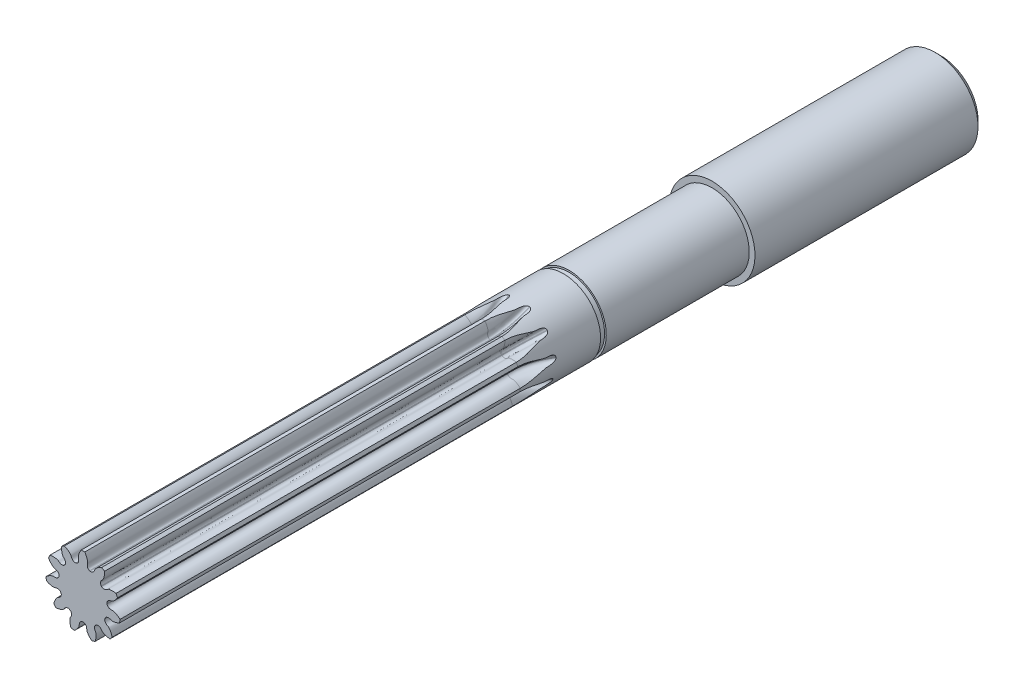
SolidWorks part; units mm, degrees
ref_plane "Спереди" through (0, 0, 0) normal (0, 0, 1) x (1, 0, 0)
ref_plane "Сверху" through (0, 0, 0) normal (0, 1, 0) x (1, 0, 0)
ref_plane "Справа" through (0, 0, 0) normal (1, 0, 0) x (0, 0, -1)
other "Configuration Table"
sketch "Эскиз1" plane through (0, 0, 0) normal (0, 0, 1) x (1, 0, 0)
  line L0 (0, 4.2505) -> (0, 6.5001) construction
  arc A6 (0.303, 6.493) -> (-0.303, 6.493) centre (0, 0) ccw
  arc A8 (3.7653, 5.2984) -> (3.2555, 5.6261) centre (0, 0) ccw
  arc A9 (6.0321, 2.4217) -> (5.7804, 2.9729) centre (0, 0) ccw
  arc A10 (6.3838, -1.224) -> (6.47, -0.6241) centre (0, 0) ccw
  arc A11 (4.7087, -4.481) -> (5.1055, -4.023) centre (0, 0) ccw
  arc A12 (1.5386, -6.3154) -> (2.12, -6.1446) centre (0, 0) ccw
  arc A13 (-2.12, -6.1446) -> (-1.5386, -6.3154) centre (0, 0) ccw
  arc A14 (-5.1055, -4.023) -> (-4.7087, -4.481) centre (0, 0) ccw
  arc A15 (-6.47, -0.6241) -> (-6.3838, -1.224) centre (0, 0) ccw
  arc A16 (-5.7804, 2.9729) -> (-6.0321, 2.4217) centre (0, 0) ccw
  arc A17 (-3.2555, 5.6261) -> (-3.7653, 5.2984) centre (0, 0) ccw
  arc A18 (-4.1999, 0.6538) -> (-4.214, 0.5559) centre (0, 0) ccw
  arc A19 (-3.1797, 2.8207) -> (-3.2445, 2.746) centre (0, 0) ccw
  arc A20 (-1.15, 4.092) -> (-1.2449, 4.0641) centre (0, 0) ccw
  arc A21 (1.2449, 4.0641) -> (1.15, 4.092) centre (0, 0) ccw
  arc A22 (3.2445, 2.746) -> (3.1797, 2.8207) centre (0, 0) ccw
  arc A23 (4.214, 0.5559) -> (4.1999, 0.6538) centre (0, 0) ccw
  arc A24 (3.8456, -1.8106) -> (3.8867, -1.7206) centre (0, 0) ccw
  arc A25 (2.2563, -3.6023) -> (2.3394, -3.5488) centre (0, 0) ccw
  arc A26 (-0.0494, -4.2502) -> (0.0494, -4.2502) centre (0, 0) ccw
  arc A27 (-2.3394, -3.5488) -> (-2.2563, -3.6023) centre (0, 0) ccw
  arc A28 (-3.8867, -1.7206) -> (-3.8456, -1.8106) centre (0, 0) ccw
  spline S0 degree 3 poles (0.303, 6.493) (0.3466, 6.4296) (0.4149, 6.3229) (0.5038, 6.1711) (0.5716, 6.0406) (0.6313, 5.9095) (0.6852, 5.7791) (0.7296, 5.6484) (0.7674, 5.5183) (0.798, 5.3728) (0.8278, 5.1961) (0.7682, 4.9723) (0.7367, 4.7556) (0.754, 4.5684) (0.7852, 4.4471) (0.829, 4.3517) (0.8776, 4.2755) (0.9328, 4.2146) (1.0177, 4.1438) (1.0937, 4.1064) (1.15, 4.092) knots 0 0 0 0 0.085617 0.14097 0.195721 0.24917 0.301247 0.352629 0.402768 0.451734 0.518548 0.599046 0.705842 0.760988 0.807057 0.844573 0.877292 0.907236 0.935686 1 1 1 1
  spline S1 degree 3 poles (-0.303, 6.493) (-0.3466, 6.4296) (-0.4149, 6.3229) (-0.5038, 6.1711) (-0.5716, 6.0406) (-0.6313, 5.9095) (-0.6852, 5.7791) (-0.7296, 5.6484) (-0.7674, 5.5183) (-0.798, 5.3728) (-0.8278, 5.1961) (-0.7682, 4.9723) (-0.7367, 4.7556) (-0.754, 4.5684) (-0.7852, 4.4471) (-0.829, 4.3517) (-0.8776, 4.2755) (-0.9328, 4.2146) (-1.0177, 4.1438) (-1.0937, 4.1064) (-1.15, 4.092) knots 0 0 0 0 0.085617 0.14097 0.195721 0.24917 0.301247 0.352629 0.402768 0.451734 0.518548 0.599046 0.705842 0.760988 0.807057 0.844573 0.877292 0.907236 0.935686 1 1 1 1
  spline S2 degree 3 poles (3.2555, 5.6261) (3.1845, 5.5963) (3.0694, 5.5435) (2.9125, 5.4638) (2.7849, 5.3907) (2.6639, 5.3126) (2.548, 5.2321) (2.4399, 5.1462) (2.3379, 5.0572) (2.2335, 4.9513) (2.1128, 4.8187) (2.042, 4.5983) (1.9513, 4.399) (1.8356, 4.2508) (1.7437, 4.1657) (1.6553, 4.1091) (1.5733, 4.0713) (1.4939, 4.0498) (1.3841, 4.0362) (1.3, 4.0458) (1.2449, 4.0641) knots 0 0 0 0 0.085617 0.14097 0.195721 0.24917 0.301247 0.352629 0.402768 0.451734 0.518548 0.599046 0.705842 0.760988 0.807057 0.844573 0.877292 0.907236 0.935686 1 1 1 1
  spline S3 degree 3 poles (3.7653, 5.2984) (3.7677, 5.2215) (3.7674, 5.0948) (3.7602, 4.9191) (3.7467, 4.7726) (3.7259, 4.6301) (3.7008, 4.4913) (3.6676, 4.3573) (3.629, 4.2274) (3.5761, 4.0885) (3.5056, 3.9237) (3.3345, 3.7676) (3.1908, 3.6024) (3.1041, 3.4356) (3.0649, 3.3166) (3.0502, 3.2127) (3.0498, 3.1224) (3.0633, 3.0412) (3.0965, 2.9357) (3.1402, 2.8632) (3.1797, 2.8207) knots 0 0 0 0 0.085617 0.14097 0.195721 0.24917 0.301247 0.352629 0.402768 0.451734 0.518548 0.599046 0.705842 0.760988 0.807057 0.844573 0.877292 0.907236 0.935686 1 1 1 1
  spline S4 degree 3 poles (5.7804, 2.9729) (5.7046, 2.9862) (5.5791, 3.004) (5.4041, 3.0219) (5.2573, 3.0293) (5.1132, 3.0291) (4.9722, 3.024) (4.8349, 3.0101) (4.7009, 2.9904) (4.5558, 2.9578) (4.3826, 2.9115) (4.2038, 2.7644) (4.0198, 2.6457) (3.8424, 2.5836) (3.719, 2.5617) (3.6141, 2.5619) (3.5246, 2.5744) (3.4462, 2.5993) (3.3465, 2.6472) (3.281, 2.7007) (3.2445, 2.746) knots 0 0 0 0 0.085617 0.14097 0.195721 0.24917 0.301247 0.352629 0.402768 0.451734 0.518548 0.599046 0.705842 0.760988 0.807057 0.844573 0.877292 0.907236 0.935686 1 1 1 1
  spline S5 degree 3 poles (6.0321, 2.4217) (5.9925, 2.3557) (5.9238, 2.2492) (5.8227, 2.1053) (5.7322, 1.9894) (5.6377, 1.8807) (5.5415, 1.7775) (5.4411, 1.6827) (5.3384, 1.5943) (5.2188, 1.5061) (5.0704, 1.4055) (4.8421, 1.3668) (4.6319, 1.3054) (4.4688, 1.212) (4.3714, 1.1331) (4.3029, 1.0537) (4.2537, 0.9778) (4.2212, 0.9023) (4.1921, 0.7956) (4.1897, 0.711) (4.1999, 0.6538) knots 0 0 0 0 0.085617 0.14097 0.195721 0.24917 0.301247 0.352629 0.402768 0.451734 0.518548 0.599046 0.705842 0.760988 0.807057 0.844573 0.877292 0.907236 0.935686 1 1 1 1
  spline S6 degree 3 poles (6.47, -0.6241) (6.4135, -0.572) (6.3176, -0.4892) (6.18, -0.3795) (6.0605, -0.2938) (5.9391, -0.2162) (5.8178, -0.1442) (5.6948, -0.0816) (5.5714, -0.0258) (5.4317, 0.0252) (5.261, 0.0799) (5.031, 0.0528) (4.812, 0.0524) (4.6292, 0.0961) (4.5136, 0.1444) (4.4254, 0.2013) (4.3569, 0.2602) (4.3044, 0.3235) (4.2465, 0.4177) (4.2203, 0.4982) (4.214, 0.5559) knots 0 0 0 0 0.085617 0.14097 0.195721 0.24917 0.301247 0.352629 0.402768 0.451734 0.518548 0.599046 0.705842 0.760988 0.807057 0.844573 0.877292 0.907236 0.935686 1 1 1 1
  spline S7 degree 3 poles (6.3838, -1.224) (6.3148, -1.2581) (6.1995, -1.3105) (6.0366, -1.3769) (5.8978, -1.4255) (5.7595, -1.4658) (5.6228, -1.5007) (5.4871, -1.5261) (5.3529, -1.5449) (5.2046, -1.5545) (5.0254, -1.5588) (4.8124, -1.468) (4.6023, -1.406) (4.4146, -1.3964) (4.2901, -1.4101) (4.1895, -1.4399) (4.1071, -1.4771) (4.0389, -1.5231) (3.9568, -1.5971) (3.909, -1.667) (3.8867, -1.7206) knots 0 0 0 0 0.085617 0.14097 0.195721 0.24917 0.301247 0.352629 0.402768 0.451734 0.518548 0.599046 0.705842 0.760988 0.807057 0.844573 0.877292 0.907236 0.935686 1 1 1 1
  spline S8 degree 3 poles (5.1055, -4.023) (5.0861, -3.9486) (5.0502, -3.827) (4.9937, -3.6604) (4.9395, -3.5237) (4.8795, -3.3928) (4.8163, -3.2667) (4.7466, -3.1475) (4.673, -3.0338) (4.5831, -2.9154) (4.469, -2.7771) (4.2609, -2.6756) (4.0765, -2.5575) (3.9463, -2.4219) (3.8751, -2.3188) (3.8317, -2.2233) (3.8059, -2.1366) (3.796, -2.055) (3.7981, -1.9445) (3.8196, -1.8626) (3.8456, -1.8106) knots 0 0 0 0 0.085617 0.14097 0.195721 0.24917 0.301247 0.352629 0.402768 0.451734 0.518548 0.599046 0.705842 0.760988 0.807057 0.844573 0.877292 0.907236 0.935686 1 1 1 1
  spline S9 degree 3 poles (4.7087, -4.481) (4.6322, -4.4724) (4.5068, -4.4542) (4.3339, -4.422) (4.1908, -4.3878) (4.0527, -4.3469) (3.9189, -4.3023) (3.791, -4.2503) (3.6679, -4.1937) (3.538, -4.1215) (3.3848, -4.0283) (3.2547, -3.8367) (3.1116, -3.671) (2.9588, -3.5615) (2.8467, -3.5057) (2.7459, -3.4763) (2.6565, -3.4631) (2.5743, -3.4649) (2.4652, -3.4828) (2.3872, -3.5157) (2.3394, -3.5488) knots 0 0 0 0 0.085617 0.14097 0.195721 0.24917 0.301247 0.352629 0.402768 0.451734 0.518548 0.599046 0.705842 0.760988 0.807057 0.844573 0.877292 0.907236 0.935686 1 1 1 1
  spline S10 degree 3 poles (2.12, -6.1446) (2.144, -6.0715) (2.1795, -5.9499) (2.222, -5.7792) (2.2503, -5.6349) (2.2706, -5.4922) (2.2856, -5.352) (2.2914, -5.214) (2.291, -5.0786) (2.2793, -4.9304) (2.2582, -4.7524) (2.138, -4.5545) (2.0467, -4.3554) (2.0105, -4.1709) (2.0063, -4.0457) (2.0215, -3.9419) (2.0466, -3.8551) (2.0824, -3.7811) (2.144, -3.6892) (2.2063, -3.6319) (2.2563, -3.6023) knots 0 0 0 0 0.085617 0.14097 0.195721 0.24917 0.301247 0.352629 0.402768 0.451734 0.518548 0.599046 0.705842 0.760988 0.807057 0.844573 0.877292 0.907236 0.935686 1 1 1 1
  spline S11 degree 3 poles (1.5386, -6.3154) (1.4789, -6.2668) (1.3833, -6.1836) (1.2552, -6.0631) (1.1533, -5.957) (1.0592, -5.8479) (0.9707, -5.738) (0.8913, -5.6252) (0.8184, -5.511) (0.7481, -5.38) (0.6696, -5.2188) (0.6638, -4.9873) (0.6329, -4.7705) (0.5636, -4.5958) (0.4995, -4.4882) (0.4306, -4.409) (0.3625, -4.3496) (0.2924, -4.3067) (0.1909, -4.2627) (0.1075, -4.2482) (0.0494, -4.2502) knots 0 0 0 0 0.085617 0.14097 0.195721 0.24917 0.301247 0.352629 0.402768 0.451734 0.518548 0.599046 0.705842 0.760988 0.807057 0.844573 0.877292 0.907236 0.935686 1 1 1 1
  spline S12 degree 3 poles (-1.5386, -6.3154) (-1.4789, -6.2668) (-1.3833, -6.1836) (-1.2552, -6.0631) (-1.1533, -5.957) (-1.0592, -5.8479) (-0.9707, -5.738) (-0.8913, -5.6252) (-0.8184, -5.511) (-0.7481, -5.38) (-0.6696, -5.2188) (-0.6638, -4.9873) (-0.6329, -4.7705) (-0.5636, -4.5958) (-0.4995, -4.4882) (-0.4306, -4.409) (-0.3625, -4.3496) (-0.2924, -4.3067) (-0.1909, -4.2627) (-0.1075, -4.2482) (-0.0494, -4.2502) knots 0 0 0 0 0.085617 0.14097 0.195721 0.24917 0.301247 0.352629 0.402768 0.451734 0.518548 0.599046 0.705842 0.760988 0.807057 0.844573 0.877292 0.907236 0.935686 1 1 1 1
  spline S13 degree 3 poles (-2.12, -6.1446) (-2.144, -6.0715) (-2.1795, -5.9499) (-2.222, -5.7792) (-2.2503, -5.6349) (-2.2706, -5.4922) (-2.2856, -5.352) (-2.2914, -5.214) (-2.291, -5.0786) (-2.2793, -4.9304) (-2.2582, -4.7524) (-2.138, -4.5545) (-2.0467, -4.3554) (-2.0105, -4.1709) (-2.0063, -4.0457) (-2.0215, -3.9419) (-2.0466, -3.8551) (-2.0824, -3.7811) (-2.144, -3.6892) (-2.2063, -3.6319) (-2.2563, -3.6023) knots 0 0 0 0 0.085617 0.14097 0.195721 0.24917 0.301247 0.352629 0.402768 0.451734 0.518548 0.599046 0.705842 0.760988 0.807057 0.844573 0.877292 0.907236 0.935686 1 1 1 1
  spline S14 degree 3 poles (-4.7087, -4.481) (-4.6322, -4.4724) (-4.5068, -4.4542) (-4.3339, -4.422) (-4.1908, -4.3878) (-4.0527, -4.3469) (-3.9189, -4.3023) (-3.791, -4.2503) (-3.6679, -4.1937) (-3.538, -4.1215) (-3.3848, -4.0283) (-3.2547, -3.8367) (-3.1116, -3.671) (-2.9588, -3.5615) (-2.8467, -3.5057) (-2.7459, -3.4763) (-2.6565, -3.4631) (-2.5743, -3.4649) (-2.4652, -3.4828) (-2.3872, -3.5157) (-2.3394, -3.5488) knots 0 0 0 0 0.085617 0.14097 0.195721 0.24917 0.301247 0.352629 0.402768 0.451734 0.518548 0.599046 0.705842 0.760988 0.807057 0.844573 0.877292 0.907236 0.935686 1 1 1 1
  spline S15 degree 3 poles (-5.1055, -4.023) (-5.0861, -3.9486) (-5.0502, -3.827) (-4.9937, -3.6604) (-4.9395, -3.5237) (-4.8795, -3.3928) (-4.8163, -3.2667) (-4.7466, -3.1475) (-4.673, -3.0338) (-4.5831, -2.9154) (-4.469, -2.7771) (-4.2609, -2.6756) (-4.0765, -2.5575) (-3.9463, -2.4219) (-3.8751, -2.3188) (-3.8317, -2.2233) (-3.8059, -2.1366) (-3.796, -2.055) (-3.7981, -1.9445) (-3.8196, -1.8626) (-3.8456, -1.8106) knots 0 0 0 0 0.085617 0.14097 0.195721 0.24917 0.301247 0.352629 0.402768 0.451734 0.518548 0.599046 0.705842 0.760988 0.807057 0.844573 0.877292 0.907236 0.935686 1 1 1 1
  spline S16 degree 3 poles (-6.3838, -1.224) (-6.3148, -1.2581) (-6.1995, -1.3105) (-6.0366, -1.3769) (-5.8978, -1.4255) (-5.7595, -1.4658) (-5.6228, -1.5007) (-5.4871, -1.5261) (-5.3529, -1.5449) (-5.2046, -1.5545) (-5.0254, -1.5588) (-4.8124, -1.468) (-4.6023, -1.406) (-4.4146, -1.3964) (-4.2901, -1.4101) (-4.1895, -1.4399) (-4.1071, -1.4771) (-4.0389, -1.5231) (-3.9568, -1.5971) (-3.909, -1.667) (-3.8867, -1.7206) knots 0 0 0 0 0.085617 0.14097 0.195721 0.24917 0.301247 0.352629 0.402768 0.451734 0.518548 0.599046 0.705842 0.760988 0.807057 0.844573 0.877292 0.907236 0.935686 1 1 1 1
  spline S17 degree 3 poles (-6.47, -0.6241) (-6.4135, -0.572) (-6.3176, -0.4892) (-6.18, -0.3795) (-6.0605, -0.2938) (-5.9391, -0.2162) (-5.8178, -0.1442) (-5.6948, -0.0816) (-5.5714, -0.0258) (-5.4317, 0.0252) (-5.261, 0.0799) (-5.031, 0.0528) (-4.812, 0.0524) (-4.6292, 0.0961) (-4.5136, 0.1444) (-4.4254, 0.2013) (-4.3569, 0.2602) (-4.3044, 0.3235) (-4.2465, 0.4177) (-4.2203, 0.4982) (-4.214, 0.5559) knots 0 0 0 0 0.085617 0.14097 0.195721 0.24917 0.301247 0.352629 0.402768 0.451734 0.518548 0.599046 0.705842 0.760988 0.807057 0.844573 0.877292 0.907236 0.935686 1 1 1 1
  spline S18 degree 3 poles (-6.0321, 2.4217) (-5.9925, 2.3557) (-5.9238, 2.2492) (-5.8227, 2.1053) (-5.7322, 1.9894) (-5.6377, 1.8807) (-5.5415, 1.7775) (-5.4411, 1.6827) (-5.3384, 1.5943) (-5.2188, 1.5061) (-5.0704, 1.4055) (-4.8421, 1.3668) (-4.6319, 1.3054) (-4.4688, 1.212) (-4.3714, 1.1331) (-4.3029, 1.0537) (-4.2537, 0.9778) (-4.2212, 0.9023) (-4.1921, 0.7956) (-4.1897, 0.711) (-4.1999, 0.6538) knots 0 0 0 0 0.085617 0.14097 0.195721 0.24917 0.301247 0.352629 0.402768 0.451734 0.518548 0.599046 0.705842 0.760988 0.807057 0.844573 0.877292 0.907236 0.935686 1 1 1 1
  spline S19 degree 3 poles (-5.7804, 2.9729) (-5.7046, 2.9862) (-5.5791, 3.004) (-5.4041, 3.0219) (-5.2573, 3.0293) (-5.1132, 3.0291) (-4.9722, 3.024) (-4.8349, 3.0101) (-4.7009, 2.9904) (-4.5558, 2.9578) (-4.3826, 2.9115) (-4.2038, 2.7644) (-4.0198, 2.6457) (-3.8424, 2.5836) (-3.719, 2.5617) (-3.6141, 2.5619) (-3.5246, 2.5744) (-3.4462, 2.5993) (-3.3465, 2.6472) (-3.281, 2.7007) (-3.2445, 2.746) knots 0 0 0 0 0.085617 0.14097 0.195721 0.24917 0.301247 0.352629 0.402768 0.451734 0.518548 0.599046 0.705842 0.760988 0.807057 0.844573 0.877292 0.907236 0.935686 1 1 1 1
  spline S20 degree 3 poles (-3.7653, 5.2984) (-3.7677, 5.2215) (-3.7674, 5.0948) (-3.7602, 4.9191) (-3.7467, 4.7726) (-3.7259, 4.6301) (-3.7008, 4.4913) (-3.6676, 4.3573) (-3.629, 4.2274) (-3.5761, 4.0885) (-3.5056, 3.9237) (-3.3345, 3.7676) (-3.1908, 3.6024) (-3.1041, 3.4356) (-3.0649, 3.3166) (-3.0502, 3.2127) (-3.0498, 3.1224) (-3.0633, 3.0412) (-3.0965, 2.9357) (-3.1402, 2.8632) (-3.1797, 2.8207) knots 0 0 0 0 0.085617 0.14097 0.195721 0.24917 0.301247 0.352629 0.402768 0.451734 0.518548 0.599046 0.705842 0.760988 0.807057 0.844573 0.877292 0.907236 0.935686 1 1 1 1
  spline S21 degree 3 poles (-3.2555, 5.6261) (-3.1845, 5.5963) (-3.0694, 5.5435) (-2.9125, 5.4638) (-2.7849, 5.3907) (-2.6639, 5.3126) (-2.548, 5.2321) (-2.4399, 5.1462) (-2.3379, 5.0572) (-2.2335, 4.9513) (-2.1128, 4.8187) (-2.042, 4.5983) (-1.9513, 4.399) (-1.8356, 4.2508) (-1.7437, 4.1657) (-1.6553, 4.1091) (-1.5733, 4.0713) (-1.4939, 4.0498) (-1.3841, 4.0362) (-1.3, 4.0458) (-1.2449, 4.0641) knots 0 0 0 0 0.085617 0.14097 0.195721 0.24917 0.301247 0.352629 0.402768 0.451734 0.518548 0.599046 0.705842 0.760988 0.807057 0.844573 0.877292 0.907236 0.935686 1 1 1 1
  point P469 (0, 0)
  point P490 (0, 0)
  dimension "D1" = 11
  dimension "D2" = 11
extrude "Бобышка-Вытянуть1" add sketch "Эскиз1" along normal blind 70
sketch "Эскиз3" plane through (0, 0, 0) normal (1, 0, 0) x (0, 0, -1)
  line L1 (0, 50) -> (0, -50) construction
  line L2 (40, 6.5) -> (40, 7.5)
  line L3 (40, 7.5) -> (79, 7.5)
  line L4 (80, 6.5) -> (80, 0)
  line L5 (80, 0) -> (0, 0)
  line L6 (0, 0) -> (0, 6.5)
  line L7 (0, 6.5) -> (14, 6.5)
  line L8 (14, 6.5) -> (14, 6.2)
  line L9 (14, 6.2) -> (15, 6.2)
  line L10 (15, 6.2) -> (15, 6.5)
  line L11 (15, 6.5) -> (40, 6.5)
  line L12 (79, 7.5) -> (80, 6.5)
  point P6 (80, 7.5)
  dimension "D1" = 80
  dimension "D2" = 25
  dimension "D3" = 40
  dimension "D4" = 7.5
  dimension "D5" = 1
  dimension "D6" = 0.3
  dimension "D7" = 6.5
  dimension "D8" = 6.5
revolve "Повернуть1" add sketch "Эскиз3" angle 360 about L5
sketch "Эскиз5" plane through (0, 0, 0) normal (0, 0, 1) x (1, 0, 0)
  line L9 (2.4864, 13.9291) -> (6.4361, 12.7693) construction
  arc A1 (4.6682, 5.8701) -> (-0.7535, 7.4621) centre (0, 0) ccw
  arc A2 (-0.7535, 7.4621) -> (0.303, 6.493) centre (3.1196, 10.6242) ccw
  arc A3 (3.2555, 5.6261) -> (4.6682, 5.8701) centre (3.1196, 10.6242) ccw
  arc A4 (1.15, 4.092) -> (1.2449, 4.0641) centre (0, 0) cw
  arc A6 (1.2449, 4.0641) -> (1.15, 4.092) centre (0, 0) ccw construction
  spline S0 degree 3 poles (1.15, 4.092) (1.0937, 4.1064) (1.0177, 4.1438) (0.9328, 4.2146) (0.8776, 4.2755) (0.829, 4.3517) (0.7852, 4.4471) (0.754, 4.5684) (0.7367, 4.7556) (0.7682, 4.9723) (0.8278, 5.1961) (0.798, 5.3728) (0.7674, 5.5183) (0.7296, 5.6484) (0.6852, 5.7791) (0.6313, 5.9095) (0.5716, 6.0406) (0.5038, 6.1711) (0.4149, 6.3229) (0.3466, 6.4296) (0.303, 6.493) knots 0 0 0 0 0.064314 0.092764 0.122708 0.155427 0.192943 0.239012 0.294158 0.400954 0.481452 0.548266 0.597232 0.647371 0.698753 0.75083 0.804279 0.85903 0.914383 1 1 1 1
  spline S1 degree 3 poles (1.2449, 4.0641) (1.3, 4.0458) (1.3841, 4.0362) (1.4939, 4.0498) (1.5733, 4.0713) (1.6553, 4.1091) (1.7437, 4.1657) (1.8356, 4.2508) (1.9513, 4.399) (2.042, 4.5983) (2.1128, 4.8187) (2.2335, 4.9513) (2.3379, 5.0572) (2.4399, 5.1462) (2.548, 5.2321) (2.6639, 5.3126) (2.7849, 5.3907) (2.9125, 5.4638) (3.0694, 5.5435) (3.1845, 5.5963) (3.2555, 5.6261) knots 0 0 0 0 0.064314 0.092764 0.122708 0.155427 0.192943 0.239012 0.294158 0.400954 0.481452 0.548266 0.597232 0.647371 0.698753 0.75083 0.804279 0.85903 0.914383 1 1 1 1
  dimension "D1" = 10.6242
  dimension "D2" = 15
revolve "Вырез-Повернуть1" cut sketch "Эскиз5" angle 360 about L9
pattern_circular "Круговой массив1" count 11 over 360 about axis through (0, 0, -80) along (0, 0, -1) of "Вырез-Повернуть1"
